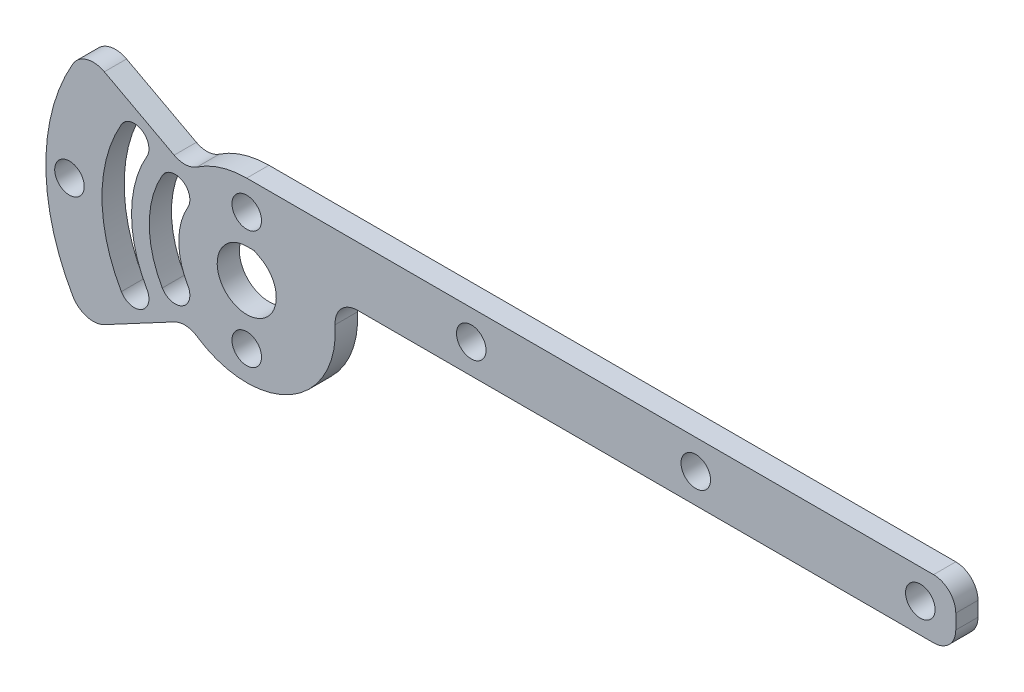
SolidWorks part; units mm, degrees
material "1060 Alloy"
ref_plane "Front Plane" through (0, 0, 0) normal (0, 0, 1) x (1, 0, 0)
ref_plane "Top Plane" through (0, 0, 0) normal (0, 1, 0) x (1, 0, 0)
ref_plane "Right Plane" through (0, 0, 0) normal (1, 0, 0) x (0, 0, -1)
sketch "Sketch1" plane through (0, 0, 0) normal (0, 0, 1) x (1, 0, 0)
  line L0 (0, 19.05) -> (152.4, 19.05)
  line L1 (152.4, 19.05) -> (152.4, 6.35)
  line L2 (0, 6.35) -> (152.4, 6.35)
  line L3 (0, 0) -> (-38.1, 0) construction
  line L4 (0, -5.08) -> (-38.1, -5.08)
  line L5 (0, 5.08) -> (-38.1, 5.08)
  line L6 (-32.9956, 19.05) -> (0, 0) construction
  line L7 (-30.6036, 23.5316) -> (2.9899, 5.602)
  line L8 (0, 0) -> (-15.3979, 8.89) construction
  line L9 (-15.3979, 8.89) -> (-24.1967, 13.97) construction
  line L10 (-24.1967, 13.97) -> (-32.9956, 19.05) construction
  line L11 (-38.1, 0) -> (0, 0)
  line L12 (-30.6036, -23.5316) -> (2.9899, -5.602)
  circle A0 centre (0, 0) radius 19.05
  circle A1 centre (0, 0) radius 6.35
  arc A2 (0, -5.08) -> (0, 5.08) centre (0, 0) ccw
  arc A3 (-38.1, 5.08) -> (-38.1, -5.08) centre (-38.1, 0) ccw
  circle A4 centre (-38.1, 0) radius 3.175
  arc A7 (-38.1, 0) -> (-32.9956, 19.05) centre (0, 0) cw construction
  arc A8 (-37.395, 21.59) -> (-43.18, 0) centre (0, 0) ccw
  arc A9 (-28.5962, 16.51) -> (-33.02, 0) centre (0, 0) ccw
  arc A10 (-28.5962, 16.51) -> (-37.395, 21.59) centre (-32.9956, 19.05) ccw
  arc A11 (-43.18, 0) -> (-33.02, 0) centre (-38.1, 0) ccw
  arc A12 (-17.78, 0) -> (-15.3979, 8.89) centre (0, 0) cw construction
  arc A13 (-18.1476, 10.4775) -> (-20.955, 0) centre (0, 0) ccw
  arc A14 (-12.6483, 7.3025) -> (-14.605, 0) centre (0, 0) ccw
  arc A15 (-12.6483, 7.3025) -> (-18.1476, 10.4775) centre (-15.3979, 8.89) ccw
  arc A16 (-20.955, 0) -> (-14.605, 0) centre (-17.78, 0) ccw
  arc A17 (-27.94, 0) -> (-24.1967, 13.97) centre (0, 0) cw construction
  arc A18 (-26.9464, 15.5575) -> (-31.115, 0) centre (0, 0) ccw
  arc A19 (-21.4471, 12.3825) -> (-24.765, 0) centre (0, 0) ccw
  arc A20 (-21.4471, 12.3825) -> (-26.9464, 15.5575) centre (-24.1967, 13.97) ccw
  arc A21 (-31.115, 0) -> (-24.765, 0) centre (-27.94, 0) ccw
  arc A22 (-17.78, 0) -> (-15.3979, -8.89) centre (0, 0) ccw construction
  arc A23 (-18.1476, -10.4775) -> (-20.955, 0) centre (0, 0) cw
  arc A24 (-12.6483, -7.3025) -> (-14.605, 0) centre (0, 0) cw
  arc A25 (-12.6483, -7.3025) -> (-18.1476, -10.4775) centre (-15.3979, -8.89) cw
  arc A26 (-20.955, 0) -> (-14.605, 0) centre (-17.78, 0) cw
  arc A27 (-27.94, 0) -> (-24.1967, -13.97) centre (0, 0) ccw construction
  arc A28 (-26.9464, -15.5575) -> (-31.115, 0) centre (0, 0) cw
  arc A29 (-21.4471, -12.3825) -> (-24.765, 0) centre (0, 0) cw
  arc A30 (-21.4471, -12.3825) -> (-26.9464, -15.5575) centre (-24.1967, -13.97) cw
  arc A31 (-31.115, 0) -> (-24.765, 0) centre (-27.94, 0) cw
  arc A32 (-38.1, 0) -> (-32.9956, -19.05) centre (0, 0) ccw construction
  arc A33 (-37.395, -21.59) -> (-43.18, 0) centre (0, 0) cw
  arc A34 (-28.5962, -16.51) -> (-33.02, 0) centre (0, 0) cw
  arc A35 (-28.5962, -16.51) -> (-37.395, -21.59) centre (-32.9956, -19.05) cw
  arc A36 (-43.18, 0) -> (-33.02, 0) centre (-38.1, 0) cw
  point P8 (-19.05, 0)
  point P18 (-17.1742, 4.6018)
  point P22 (-36.8018, 9.861)
  point P37 (-26.988, 7.2314)
  point P50 (-17.1742, -4.6018)
  point P57 (-26.988, -7.2314)
  point P63 (-36.8018, -9.861)
  dimension "D1" = 12.7
  dimension "D4" = 5.08
  dimension "D8" = 6.35
  dimension "D6" = 27.94
  dimension "D7" = 17.78
  dimension "D2" = 12.7
  dimension "D3" = 152.4
  dimension "D5" = 38.1
  dimension "D9" = 30
  dimension "D10" = 152.4
extrude "Boss-Extrude1" add sketch "Sketch1" along normal blind 4.7752
fillet "Fillet1" radius 4.7752 5 edges at (17.9605, 6.35, 2.3876) (-12.855, -14.0588, 2.3876) (-12.855, 14.0588, 2.3876) (152.4, 19.05, 2.3876) (152.4, 6.35, 2.3876)
sketch "Sketch2" plane through (0, 0, 4.7752) normal (0, 0, 1) x (1, 0, 0)
  line L0 (0, 12.7) -> (0, 0) construction
  line L1 (0, 0) -> (0, -12.7) construction
  line L2 (-38.1, 0) -> (0, 0) construction
  circle A0 centre (0, 12.7) radius 3.175
  circle A1 centre (0, -12.7) radius 3.175
  circle A3 centre (48.26, 12.7) radius 3.175
  circle A4 centre (96.52, 12.7) radius 3.175
  circle A5 centre (144.78, 12.7) radius 3.175
  arc A6 (-18.1476, -10.4775) -> (-12.6483, -7.3025) centre (-15.3979, -8.89) ccw construction
  circle A7 centre (-38.1, 0) radius 3.175 construction
  dimension "D1" = 12.7
  dimension "D2" = 4
extrude "Cut-Extrude2" cut sketch "Sketch2" against normal blind 12.6492
